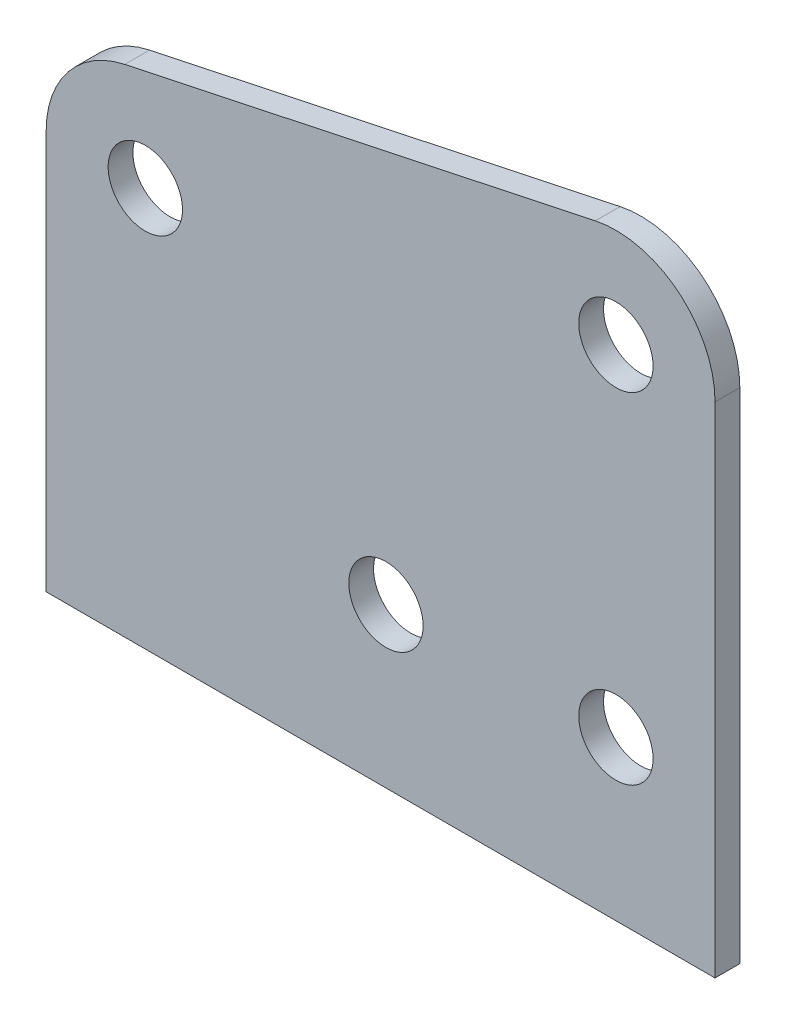
SolidWorks part; units mm, degrees
ref_plane "Front Plane" through (0, 0, 0) normal (0, 0, 1) x (1, 0, 0)
ref_plane "Top Plane" through (0, 0, 0) normal (0, 1, 0) x (1, 0, 0)
ref_plane "Right Plane" through (0, 0, 0) normal (1, 0, 0) x (0, 0, -1)
sketch "Sketch1" plane through (0, 0, 0) normal (0, 0, 1) x (1, 0, 0)
  line L0 (0, 0) -> (20.6877, 0) construction
  line L1 (20.6877, 0) -> (20.6877, 20.3568) construction
  line L2 (20.6877, 20.3568) -> (20.6877, 63.9178) construction
  line L3 (20.6877, 20.3568) -> (-8.7763, 20.3568) construction
  line L4 (-8.7763, 20.3568) -> (-39.6056, 20.3568) construction
  line L5 (-39.6056, 20.3568) -> (-39.6056, 51.1312) construction
  line L6 (18.0529, 76.3415) -> (-42.2403, 63.5549)
  line L7 (-52.3056, 51.1312) -> (-52.3056, 0)
  line L8 (33.3877, 63.9178) -> (33.3877, 0)
  line L9 (-52.3056, 0) -> (33.3877, 0)
  circle A0 centre (20.6877, 20.3568) radius 4.7625
  circle A1 centre (20.6877, 63.9178) radius 4.7625
  circle A2 centre (-8.7763, 20.3568) radius 4.7625
  circle A3 centre (-39.6056, 51.1312) radius 4.7625
  arc A4 (33.3877, 63.9178) -> (18.0529, 76.3415) centre (20.6877, 63.9178) ccw
  arc A5 (-42.2403, 63.5549) -> (-52.3056, 51.1312) centre (-39.6056, 51.1312) ccw
  dimension "D2" = 9.525
  dimension "D4" = 9.525
  dimension "D5" = 9.525
  dimension "D7" = 9.525
  dimension "D10" = 25.4
  dimension "D11" = 25.4
  dimension "D1" = 20.3568
  dimension "D3" = 43.561
  dimension "D6" = 29.464
  dimension "D8" = 30.8293
  dimension "D9" = 30.7744
extrude "Boss-Extrude1" add sketch "Sketch1" along normal blind 3.175
